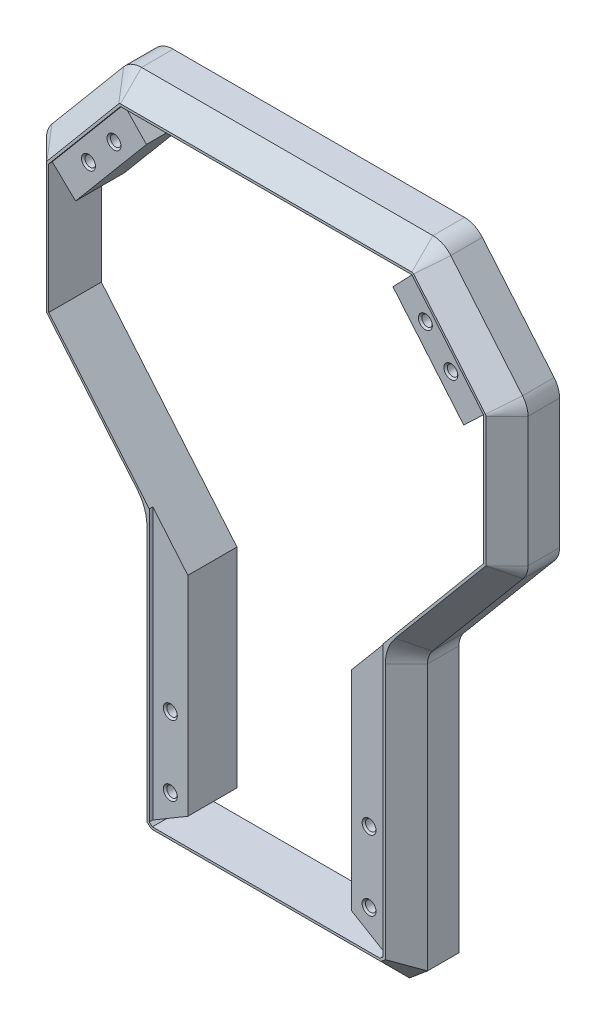
SolidWorks part; units mm, degrees
ref_plane "Plano frontal" through (0, 0, 0) normal (0, 0, 1) x (1, 0, 0)
ref_plane "Plano superior" through (0, 0, 0) normal (0, 1, 0) x (1, 0, 0)
ref_plane "Plano direito" through (0, 0, 0) normal (1, 0, 0) x (0, 0, -1)
sketch "Esboço1" plane through (0, 0, 0) normal (0, 0, 1) x (1, 0, 0)
  line L0 (-62.3014, 279.4996) -> (62.3014, 279.4996)
  line L1 (-60, 5.9442) -> (-60, 119.6802)
  line L2 (-62.1215, 125.509) -> (-100.8785, 171.6978)
  line L3 (-103, 177.5265) -> (-103, 232.9144)
  line L4 (-52.7216, 259.4996) -> (52.7216, 259.4996)
  line L5 (0, 279.4996) -> (0, 0) construction
  line L6 (-69.9619, 275.9274) -> (-100.6604, 239.3423)
  line L7 (-83, 181.5055) -> (-83, 223.4152)
  line L8 (-83, 223.4152) -> (-52.7216, 259.4996)
  line L9 (-35, 19.4996) -> (35, 19.4996)
  line L10 (-35, 19.4996) -> (-35, 124.3013)
  line L11 (-35, 124.3013) -> (-83, 181.5055)
  line L12 (-60, 5.9442) -> (-52.3196, -0.5004)
  line L13 (-52.3196, -0.5004) -> (52.3196, -0.5004)
  line L14 (60, 5.9442) -> (52.3196, -0.5004)
  line L15 (35, 124.3013) -> (83, 181.5055)
  line L16 (35, 19.4996) -> (35, 124.3013)
  line L17 (83, 223.4152) -> (52.7216, 259.4996)
  line L18 (83, 181.5055) -> (83, 223.4152)
  line L19 (69.9619, 275.9274) -> (100.6604, 239.3423)
  line L20 (103, 177.5265) -> (103, 232.9144)
  line L21 (62.1215, 125.509) -> (100.8785, 171.6978)
  line L22 (60, 5.9442) -> (60, 119.6802)
  arc A0 (-103, 232.9144) -> (-100.6604, 239.3423) centre (-93, 232.9144) cw
  arc A1 (-100.8785, 171.6978) -> (-103, 177.5265) centre (-93.9321, 177.5265) cw
  arc A2 (-60, 119.6802) -> (-62.1215, 125.509) centre (-69.0679, 119.6802) ccw
  arc A3 (62.3014, 279.4996) -> (69.9619, 275.9274) centre (62.3014, 269.4996) cw
  arc A4 (-62.3014, 279.4996) -> (-69.9619, 275.9274) centre (-62.3014, 269.4996) ccw
  arc A5 (60, 119.6802) -> (62.1215, 125.509) centre (69.0679, 119.6802) cw
  arc A6 (100.8785, 171.6978) -> (103, 177.5265) centre (93.9321, 177.5265) ccw
  arc A7 (103, 232.9144) -> (100.6604, 239.3423) centre (93, 232.9144) ccw
  point P27 (-103, 236.5541)
  point P33 (0, 19.4996)
  point P35 (0, -0.5004)
  point P40 (0, 259.4996)
  point P45 (0, 19.4996)
  point P46 (0, 19.4996)
  point P48 (0, 259.4996)
  point P53 (0, 280)
  dimension "D7" = 40
  dimension "D12" = 10
  dimension "D14" = 10
  dimension "D16" = 20
  dimension "D5" = 40
  dimension "D2" = 103
  dimension "D3" = 20
  dimension "D4" = 60
  dimension "D6" = 40
  dimension "D8" = 20
  dimension "D9" = 280
  dimension "D10" = 25
  dimension "D13" = 40
  dimension "D15" = 20
  dimension "D18" = 57.2042
extrude "Ressalto-extrusão1" add sketch "Esboço1" along normal mid plane 45
chamfer "Chanfro1" distance 9 angle 45 20 edges at (0, -0.5004, 22.5) (-60, 62.8122, 22.5) (-60.5469, 122.7816, 22.5) (-81.5, 148.6034, 22.5) (0, 279.4996, 22.5) (-102.4531, 174.4251, 22.5) (-85.3112, 257.6349, 22.5) (-103, 205.2205, 22.5) (60.5469, 122.7816, 22.5) (66.5276, 278.5626, 22.5) (-66.5276, 278.5626, 22.5) (-102.3969, 236.3346, 22.5) (-56.1598, 2.7219, 22.5) (85.3112, 257.6349, 22.5) (102.3969, 236.3346, 22.5) (103, 205.2205, 22.5) (102.4531, 174.4251, 22.5) (81.5, 148.6034, 22.5) (60, 62.8122, 22.5) (56.1598, 2.7219, 22.5)
sketch "Esboço3" plane through (0, 0, 0) normal (0, 0, 1) x (1, 0, 0)
  line L1 (-722.7729, 507.4347) -> (416.458, 507.4347)
  line L2 (-722.7729, 507.4347) -> (-722.7729, -202.3634)
  line L3 (-722.7729, -202.3634) -> (416.458, -202.3634)
  line L4 (416.458, 507.4347) -> (416.458, -202.3634)
extrude "Corte-extrusão1" cut sketch "Esboço3" against normal up to next
sketch "Esboço4" plane through (0, 0, 22.5) normal (0, 0, 1) x (1, 0, 0)
  line L0 (35, 19.4996) -> (-35, 19.4996)
  line L1 (-35, 19.4996) -> (35, 19.4996) construction
  line L2 (62.3014, 270.4996) -> (-62.3014, 270.4996) construction
  line L3 (-35, 19.4996) -> (-35, 124.3013)
  line L4 (-35, 19.4996) -> (-35, 124.3013) construction
  line L5 (0, -6.7811) -> (0, 343.2781) construction
  line L6 (-35, 124.3013) -> (-83, 181.5055)
  line L8 (-83, 181.5055) -> (-83, 223.4152)
  line L9 (-83, 223.4152) -> (-52.7216, 259.4996)
  line L11 (-52.7216, 259.4996) -> (52.7216, 259.4996)
  line L12 (-52.7216, 259.4996) -> (52.7216, 259.4996) construction
  line L13 (62.3014, 269.4996) -> (-62.3014, 269.4996)
  line L14 (-62.3014, 269.4996) -> (-93, 232.9144)
  line L15 (-93, 232.9144) -> (-93, 177.8658)
  line L16 (-93, 177.8658) -> (-50, 126.6204)
  line L18 (-50, 126.6204) -> (-50, 10.6073)
  line L19 (-50, 10.6073) -> (-48.6799, 9.4996)
  line L20 (-48.6799, 9.4996) -> (48.6799, 9.4996)
  line L22 (-63.0675, 270.1423) -> (-93.766, 233.5572) construction
  line L24 (-94, 232.9144) -> (-94, 177.5265) construction
  line L25 (-51, 119.6802) -> (-51, 10.141) construction
  line L26 (-49.0438, 8.4996) -> (49.0438, 8.4996) construction
  line L27 (-93.9841, 177.4829) -> (-55.2271, 131.294) construction
  line L32 (-51, 10.141) -> (-49.0438, 8.4996) construction
  line L33 (50, 10.6073) -> (48.6799, 9.4996)
  line L34 (50, 126.6204) -> (50, 10.6073)
  line L35 (93, 177.8658) -> (50, 126.6204)
  line L36 (93, 232.9144) -> (93, 177.8658)
  line L37 (62.3014, 269.4996) -> (93, 232.9144)
  line L38 (83, 223.4152) -> (52.7216, 259.4996)
  line L39 (83, 181.5055) -> (83, 223.4152)
  line L40 (35, 124.3013) -> (83, 181.5055)
  line L41 (35, 19.4996) -> (35, 124.3013)
  point P40 (0, 9.4996)
  point P44 (0, 269.4996)
  point P45 (0, 259.4996)
  point P46 (0, 19.4996)
  dimension "D1" = 1
  dimension "D2" = 1
  dimension "D3" = 1
  dimension "D4" = 1
  dimension "D5" = 1
  dimension "D6" = 1
  dimension "D7" = 1
extrude "Corte-extrusão5" cut sketch "Esboço4" against normal blind 1.5
sketch "Esboço5" plane through (0, 0, 21) normal (0, 0, 1) x (1, 0, 0)
  line L0 (-93, 232.9144) -> (-83, 223.4152)
  line L1 (-83, 223.4152) -> (-83, 181.5055)
  line L2 (-83, 181.5055) -> (-35, 124.3013)
  line L3 (-93, 177.8658) -> (-93, 232.9144)
  line L4 (-35, 124.3013) -> (-35, 19.4996) construction
  line L5 (-35, 108.7441) -> (-93, 177.8658)
  line L6 (0, -17.6729) -> (0, 329.9726) construction
  line L7 (-52.7216, 259.4996) -> (-62.3014, 269.4996)
  line L8 (-62.3014, 269.4996) -> (62.3014, 269.4996)
  line L9 (62.3014, 269.4996) -> (-62.3014, 269.4996) construction
  line L10 (-52.7216, 259.4996) -> (52.7216, 259.4996)
  line L11 (52.7216, 259.4996) -> (-52.7216, 259.4996) construction
  line L12 (-50, 10.6073) -> (-35, 19.4996)
  line L13 (-35, 19.4996) -> (35, 19.4996)
  line L14 (35, 19.4996) -> (-35, 19.4996) construction
  line L15 (-50, 10.6073) -> (-48.6799, 9.4996)
  line L16 (-48.6799, 9.4996) -> (48.6799, 9.4996)
  line L17 (-48.6799, 9.4996) -> (48.6799, 9.4996) construction
  line L18 (50, 10.6073) -> (48.6799, 9.4996)
  line L19 (50, 10.6073) -> (35, 19.4996)
  line L20 (52.7216, 259.4996) -> (62.3014, 269.4996)
  line L21 (35, 108.7441) -> (93, 177.8658)
  line L22 (35, 124.3013) -> (35, 108.7441)
  line L23 (93, 177.8658) -> (93, 232.9144)
  line L24 (83, 181.5055) -> (35, 124.3013)
  line L25 (83, 223.4152) -> (83, 181.5055)
  line L26 (93, 232.9144) -> (83, 223.4152)
  line L29 (-93, 177.8658) -> (-50, 126.6204) construction
  line L30 (-35, 108.7441) -> (-35, 124.3013)
  point P38 (0, 9.4996)
  point P40 (0, 19.4996)
  point P41 (0, 259.4996)
  point P42 (0, 269.4996)
extrude "Corte-extrusão6" cut sketch "Esboço5" against normal up to next
sketch "Esboço7" plane through (0, 0, 22.5) normal (0, 0, 1) x (1, 0, 0)
  line L0 (-62.3014, 269.4996) -> (-93, 232.9144) construction
  line L1 (-50, 126.6204) -> (-50, 10.6073) construction
  line L2 (-50, 126.6204) -> (-50, 10.6073) construction
  line L3 (-48.6799, 9.4996) -> (48.6799, 9.4996) construction
  line L4 (62.3014, 269.4996) -> (-62.3014, 269.4996) construction
  line L5 (0, -30.1101) -> (0, 304.4524) construction
  circle A0 centre (-42.5, 24.4996) radius 2
  circle A1 centre (-42.5, 54.4996) radius 2
  circle A2 centre (-66.5892, 253.4996) radius 2
  circle A3 centre (-77.4975, 240.4996) radius 2
  circle A4 centre (77.4975, 240.4996) radius 2
  circle A5 centre (66.5892, 253.4996) radius 2
  circle A6 centre (42.5, 54.4996) radius 2
  circle A7 centre (42.5, 24.4996) radius 2
  dimension "D1" = 7
  dimension "D2" = 7
  dimension "D3" = 7.5
  dimension "D4" = 7.5
  dimension "D5" = 15
  dimension "D6" = 30
  dimension "D8" = 29
  dimension "D7" = 16
hole_wizard "Escareado para parafuso Allen sextavado escareado de M41" positions "3DSketch1" profile "Esboço8" countersink size "M4" standard "ISO" end condition through all
sketch3d "3DSketch1"
  point P0 (-66.5892, 253.4996, 22.5)
  point P3 (-77.4975, 240.4996, 22.5)
  point P6 (66.5892, 253.4996, 22.5)
  point P9 (77.4975, 240.4996, 22.5)
  point P12 (-42.5, 54.4996, 22.5)
  point P15 (-42.5, 24.4996, 22.5)
  point P18 (42.5, 24.4996, 22.5)
  point P21 (42.5, 54.4996, 22.5)
sketch "Esboço8" plane through (-66.5892, 253.4996, 22.5) normal (1, 0, 0) x (0, -1, 0)
  line L0 (0, 0) -> (0, 22.5)
  line L1 (0, 22.5) -> (2.25, 22.5)
  line L2 (2.25, 22.5) -> (2.25, 2.23)
  line L3 (2.25, 2.23) -> (4.48, 0)
  line L5 (4.48, 0) -> (0, 0)
  line L6 (-2.25, 2.23) -> (-4.48, 0) construction
  line L11 (0, -6.35) -> (0, 107.95) construction
  dimension "Thru Hole Dia." = 4.5
  dimension "Thru Hole Depth" = 22.5
  dimension "Near C'Sink Dia." = 8.96
  dimension "Near C'Sink Angle" = 90
sketch "Esboço9" plane through (0, 0, 0) normal (0, 0, -1) x (-1, 0, 0)
  line L0 (0, -16.6147) -> (0, 337.6584) construction
  line L1 (-66.5892, 257.541) -> (-70.0892, 255.5203)
  line L2 (-70.0892, 255.5203) -> (-70.0892, 251.4788)
  line L3 (-70.0892, 251.4788) -> (-66.5892, 249.4581)
  line L4 (-66.5892, 249.4581) -> (-63.0892, 251.4788)
  line L5 (-63.0892, 251.4788) -> (-63.0892, 255.5203)
  line L6 (-63.0892, 255.5203) -> (-66.5892, 257.541)
  line L7 (-77.4975, 244.541) -> (-80.9975, 242.5203)
  line L8 (-80.9975, 242.5203) -> (-80.9975, 238.4788)
  line L9 (-80.9975, 238.4788) -> (-77.4975, 236.4581)
  line L10 (-77.4975, 236.4581) -> (-73.9975, 238.4788)
  line L11 (-73.9975, 238.4788) -> (-73.9975, 242.5203)
  line L12 (-73.9975, 242.5203) -> (-77.4975, 244.541)
  line L13 (-42.5, 58.541) -> (-46, 56.5203)
  line L14 (-46, 56.5203) -> (-46, 52.4788)
  line L15 (-46, 52.4788) -> (-42.5, 50.4581)
  line L16 (-42.5, 50.4581) -> (-39, 52.4788)
  line L17 (-39, 52.4788) -> (-39, 56.5203)
  line L18 (-39, 56.5203) -> (-42.5, 58.541)
  line L19 (-42.5, 28.541) -> (-46, 26.5203)
  line L20 (-46, 26.5203) -> (-46, 22.4788)
  line L21 (-46, 22.4788) -> (-42.5, 20.4581)
  line L22 (-42.5, 20.4581) -> (-39, 22.4788)
  line L23 (-39, 22.4788) -> (-39, 26.5203)
  line L24 (-39, 26.5203) -> (-42.5, 28.541)
  line L25 (39, 26.5203) -> (42.5, 28.541)
  line L26 (39, 22.4788) -> (39, 26.5203)
  line L27 (42.5, 20.4581) -> (39, 22.4788)
  line L28 (46, 22.4788) -> (42.5, 20.4581)
  line L29 (46, 26.5203) -> (46, 22.4788)
  line L30 (42.5, 28.541) -> (46, 26.5203)
  line L31 (39, 56.5203) -> (42.5, 58.541)
  line L32 (39, 52.4788) -> (39, 56.5203)
  line L33 (42.5, 50.4581) -> (39, 52.4788)
  line L34 (46, 52.4788) -> (42.5, 50.4581)
  line L35 (46, 56.5203) -> (46, 52.4788)
  line L36 (42.5, 58.541) -> (46, 56.5203)
  line L37 (73.9975, 242.5203) -> (77.4975, 244.541)
  line L38 (73.9975, 238.4788) -> (73.9975, 242.5203)
  line L39 (77.4975, 236.4581) -> (73.9975, 238.4788)
  line L40 (80.9975, 238.4788) -> (77.4975, 236.4581)
  line L41 (80.9975, 242.5203) -> (80.9975, 238.4788)
  line L42 (77.4975, 244.541) -> (80.9975, 242.5203)
  line L43 (63.0892, 255.5203) -> (66.5892, 257.541)
  line L44 (63.0892, 251.4788) -> (63.0892, 255.5203)
  line L45 (66.5892, 249.4581) -> (63.0892, 251.4788)
  line L46 (70.0892, 251.4788) -> (66.5892, 249.4581)
  line L47 (70.0892, 255.5203) -> (70.0892, 251.4788)
  line L48 (66.5892, 257.541) -> (70.0892, 255.5203)
  circle A0 centre (-66.5892, 253.4996) radius 3.5 construction
  circle A1 centre (-77.4975, 240.4996) radius 3.5 construction
  circle A2 centre (-42.5, 54.4996) radius 3.5 construction
  circle A3 centre (-42.5, 24.4996) radius 3.5 construction
  circle A4 centre (42.5, 24.4996) radius 3.5 construction
  circle A5 centre (42.5, 54.4996) radius 3.5 construction
  circle A6 centre (77.4975, 240.4996) radius 3.5 construction
  circle A7 centre (66.5892, 253.4996) radius 3.5 construction
extrude "Corte-extrusão7" cut sketch "Esboço9" against normal blind 10
